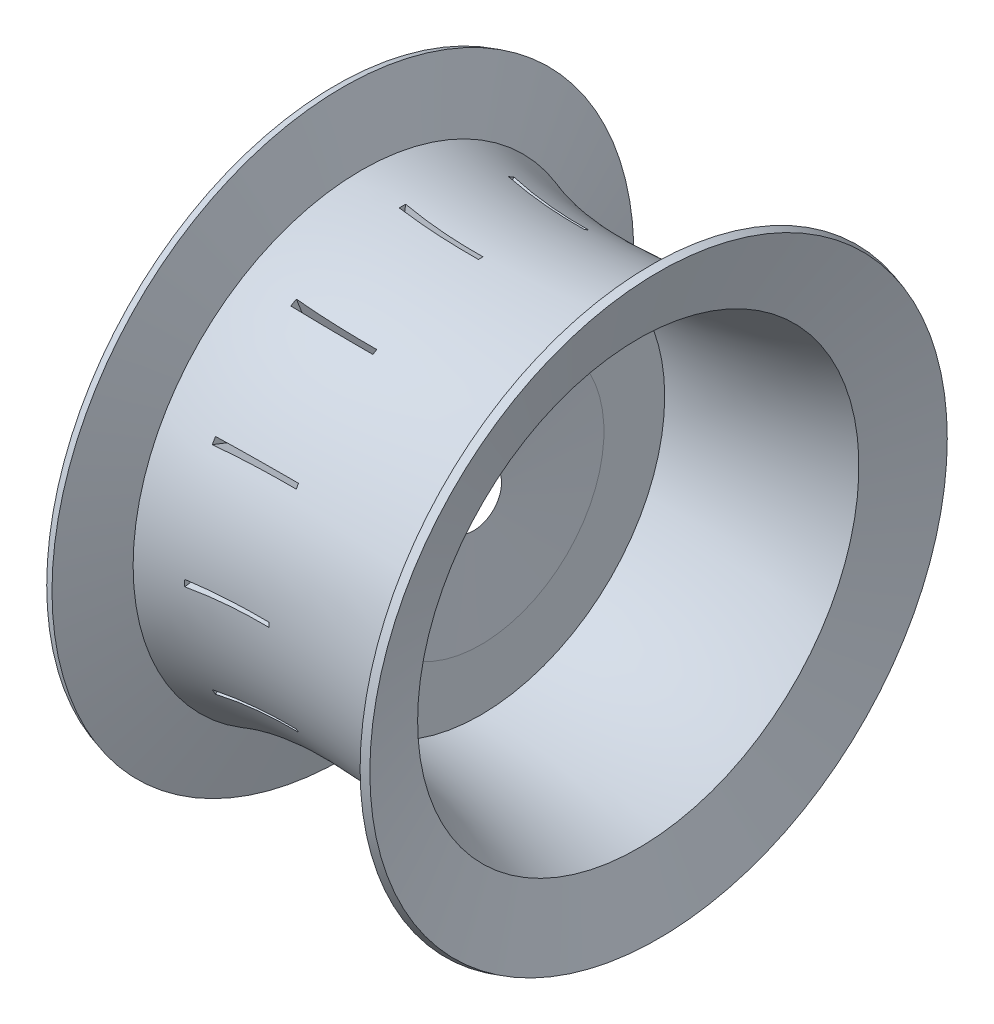
SolidWorks part; units mm, degrees
material "6063-O"
ref_plane "Front Plane" through (0, 0, 0) normal (0, 0, 1) x (1, 0, 0)
ref_plane "Top Plane" through (0, 0, 0) normal (0, 1, 0) x (1, 0, 0)
ref_plane "Right Plane" through (0, 0, 0) normal (1, 0, 0) x (0, 0, -1)
sketch "Sketch1" plane through (0, 0, 0) normal (0, 0, 1) x (1, 0, 0)
  line L0 (0, 94.4296) -> (0, -9) construction
  line L1 (-165.2947, 0) -> (132.5595, 0) construction
  line L2 (-50, 94.4296) -> (50, 94.4296) construction
  line L3 (-50, 94.4296) -> (-43.9501, 74.1465)
  line L4 (50, 94.4296) -> (43.9501, 74.1465)
  line L5 (-52.434, 93.7036) -> (-45.843, 71.6065)
  line L6 (52.434, 93.7036) -> (45.843, 71.6065)
  line L7 (-52.434, 93.7036) -> (-50, 94.4296)
  line L8 (50, 94.4296) -> (52.434, 93.7036)
  line L9 (-43.9501, 74.1465) -> (43.9501, 74.1465) construction
  line L10 (-45.843, 71.6065) -> (45.843, 71.6065) construction
  line L12 (-7.5245, 59.7908) -> (-7.5245, 9)
  line L13 (-5.2917, 59.7177) -> (-5.2917, 40)
  line L14 (-7.5245, 9) -> (-5.2917, 40)
  spline S0 degree 3 poles (-43.9501, 74.1465) (-30.3248, 69.5275) (-7.9353, 64.636) (43.9501, 74.1465) knots 0 0 0 0 1 1 1 1
  spline S1 degree 3 poles (-45.843, 71.6065) (-27.0718, 58.1624) (-31.4639, 60.5135) (-7.5245, 59.7908) knots 0 0 0 0 0.445816 0.445816 0.445816 0.445816
  spline S2 degree 2 poles (-5.2917, 59.7177) (20.8618, 60.269) (45.843, 71.6065) knots 0.463836 0.463836 0.463836 1 1 1
  dimension "D1" = 50
  dimension "D2" = 9
  dimension "D3" = 50
  dimension "D4" = 2.54
  dimension "D5" = 9
  dimension "D6" = 40
revolve "Revolve1" add sketch "Sketch1" angle 360 about L1
sketch "Sketch2" plane through (-5.2917, 0, 0) normal (1, 0, 0) x (0, 0, -1)
  line L0 (0, 131.7329) -> (0, 63.9583) construction
  line L1 (0, 63.9583) -> (-9.0834, 122.2992)
  line L2 (0, 63.9583) -> (9.0834, 122.2992)
  line L3 (-9.0834, 122.2992) -> (9.0834, 122.2992)
  line L4 (31.9792, 55.3895) -> (53.2831, 110.4559)
  line L5 (53.2831, 110.4559) -> (69.0161, 101.3725)
  line L6 (31.9792, 55.3895) -> (69.0161, 101.3725)
  line L7 (55.3895, 31.9792) -> (101.3725, 69.0161)
  line L8 (101.3725, 69.0161) -> (110.4559, 53.2831)
  line L9 (55.3895, 31.9792) -> (110.4559, 53.2831)
  line L10 (63.9583, 0) -> (122.2992, 9.0834)
  line L11 (122.2992, 9.0834) -> (122.2992, -9.0834)
  line L12 (63.9583, 0) -> (122.2992, -9.0834)
  line L13 (55.3895, -31.9792) -> (110.4559, -53.2831)
  line L14 (110.4559, -53.2831) -> (101.3725, -69.0161)
  line L15 (55.3895, -31.9792) -> (101.3725, -69.0161)
  line L16 (31.9792, -55.3895) -> (69.0161, -101.3725)
  line L17 (69.0161, -101.3725) -> (53.2831, -110.4559)
  line L18 (31.9792, -55.3895) -> (53.2831, -110.4559)
  line L19 (0, -63.9583) -> (9.0834, -122.2992)
  line L20 (9.0834, -122.2992) -> (-9.0834, -122.2992)
  line L21 (0, -63.9583) -> (-9.0834, -122.2992)
  line L22 (-31.9792, -55.3895) -> (-53.2831, -110.4559)
  line L23 (-53.2831, -110.4559) -> (-69.0161, -101.3725)
  line L24 (-31.9792, -55.3895) -> (-69.0161, -101.3725)
  line L25 (-55.3895, -31.9792) -> (-101.3725, -69.0161)
  line L26 (-101.3725, -69.0161) -> (-110.4559, -53.2831)
  line L27 (-55.3895, -31.9792) -> (-110.4559, -53.2831)
  line L28 (-63.9583, 0) -> (-122.2992, -9.0834)
  line L29 (-122.2992, -9.0834) -> (-122.2992, 9.0834)
  line L30 (-63.9583, 0) -> (-122.2992, 9.0834)
  line L31 (-55.3895, 31.9792) -> (-110.4559, 53.2831)
  line L32 (-110.4559, 53.2831) -> (-101.3725, 69.0161)
  line L33 (-55.3895, 31.9792) -> (-101.3725, 69.0161)
  line L34 (-31.9792, 55.3895) -> (-69.0161, 101.3725)
  line L35 (-69.0161, 101.3725) -> (-53.2831, 110.4559)
  line L36 (-31.9792, 55.3895) -> (-53.2831, 110.4559)
  circle A0 centre (0, 0) radius 87.8612
  point P43 (0, 0)
  dimension "D1" = 12
extrude "Cut-Extrude1" cut sketch "Sketch2" against normal blind 25.4 contours L35 L36 L34 | L31 L32 L33 | L28 L29 L30 | L26 L27 L25 | L22 L23 L24 | L19 L20 L21 | L17 L18 L16 | L14 L15 L13 | L10 L11 L12 | L8 L9 L7 | L4 L5 L6 | L2 L3 L1
